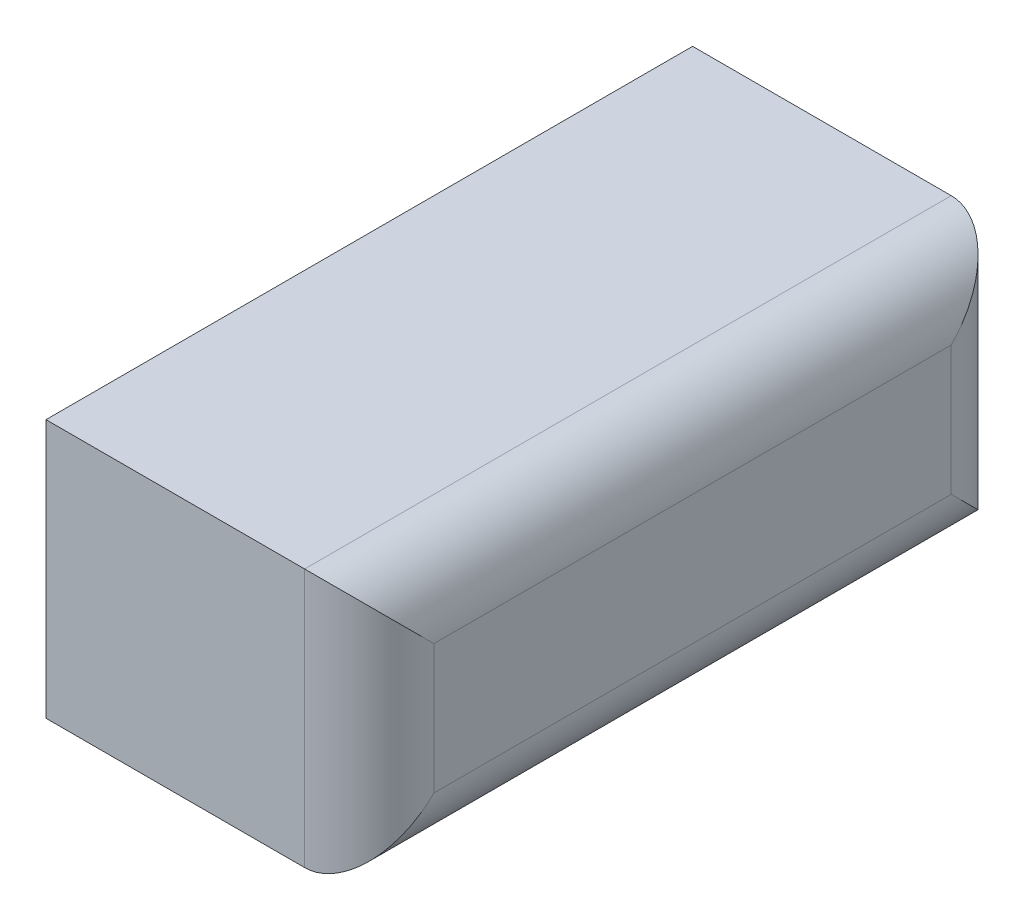
SolidWorks part; units mm, degrees
ref_plane "Plan de face" through (0, 0, 0) normal (0, 0, 1) x (1, 0, 0)
ref_plane "Plan de dessus" through (0, 0, 0) normal (0, 1, 0) x (1, 0, 0)
ref_plane "Plan de droite" through (0, 0, 0) normal (1, 0, 0) x (0, 0, -1)
sketch "Esquisse1" plane through (0, 0, 0) normal (0, 1, 0) x (1, 0, 0)
  line L1 (0, 0) -> (0.5, 0)
  line L2 (0, 0) -> (0, 1)
  line L3 (0, 1) -> (0.5, 1)
  line L4 (0.5, 0) -> (0.5, 1)
  dimension "D1" = 1
  dimension "D2" = 0.5
extrude "Extrusion1" add sketch "Esquisse1" along normal blind 0.4
fillet "Congé1" radius 0.1 4 edges at (0.5, 0.2, 0) (0.5, 0.4, -0.5) (0.5, 0.2, -1) (0.5, 0, -0.5)
